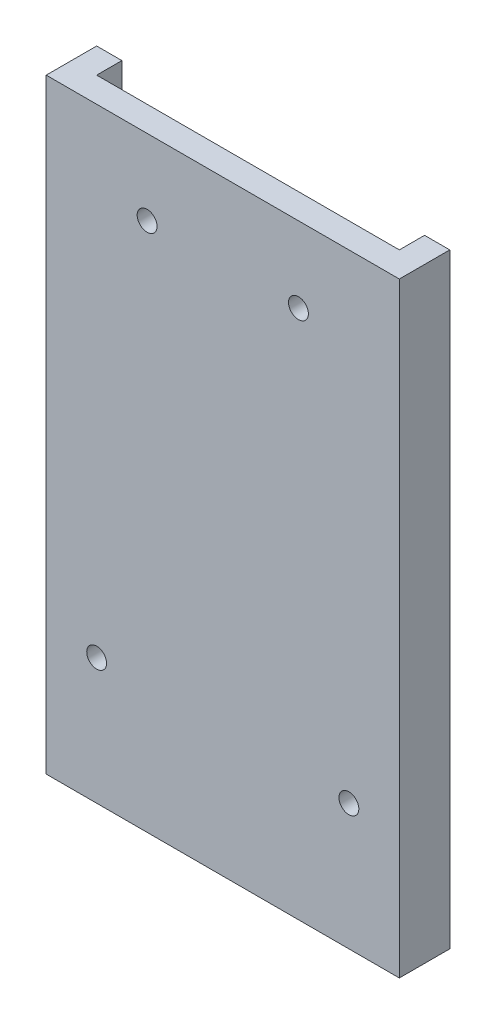
SolidWorks part; units mm, degrees
material "ABS"
ref_plane "Front" through (0, 0, 0) normal (0, 0, 1) x (1, 0, 0)
ref_plane "Top" through (0, 0, 0) normal (0, 1, 0) x (1, 0, 0)
ref_plane "Right" through (0, 0, 0) normal (1, 0, 0) x (0, 0, -1)
sketch "Sketch1" plane through (0, 0, 0) normal (0, 1, 0) x (1, 0, 0)
  line L1 (-22.225, 3.175) -> (22.225, 3.175)
  line L2 (-22.225, 3.175) -> (-22.225, -3.175)
  line L3 (-22.225, -3.175) -> (22.225, -3.175)
  line L4 (22.225, 3.175) -> (22.225, -3.175)
  line L5 (-22.225, 3.175) -> (22.225, -3.175) construction
  line L6 (-22.225, -3.175) -> (22.225, 3.175) construction
  point P0 (0, 0)
  dimension "D1" = 44.45
  dimension "D2" = 6.35
extrude "Boss-Extrude1" add sketch "Sketch1" along normal blind 76.2
sketch "Sketch2" plane through (0, 76.2, 0) normal (0, 1, 0) x (1, 0, 0)
  line L0 (22.225, 3.175) -> (-22.225, 3.175) construction
  line L1 (-19.05, 3.175) -> (19.05, 3.175)
  line L2 (-19.05, 3.175) -> (-19.05, 0)
  line L3 (-19.05, 0) -> (19.05, 0)
  line L4 (19.05, 3.175) -> (19.05, 0)
  dimension "D1" = 38.1
extrude "Cut-Extrude1" cut sketch "Sketch2" against normal offset from surface (73.025 mm away) 3.175 up to face at (0, 0, 0)
sketch "Sketch4" plane through (0, 0, 0) normal (0, 0, -1) x (-1, 0, 0)
  line L0 (-19.05, 15.875) -> (19.05, 15.875) construction
  line L1 (-19.05, 3.175) -> (-19.05, 76.2) construction
  line L2 (19.05, 3.175) -> (19.05, 76.2) construction
  line L3 (-19.05, 66.675) -> (19.05, 66.675) construction
  line L4 (19.05, 3.175) -> (19.05, 76.2) construction
  line L5 (-19.05, 3.175) -> (19.05, 3.175) construction
  line L6 (-15.875, 15.875) -> (-9.525, 66.675) construction
  line L7 (9.525, 66.675) -> (15.875, 15.875) construction
  line L8 (-12.7, 41.275) -> (12.7, 41.275) construction
  circle A0 centre (-9.525, 66.675) radius 1.25
  circle A1 centre (9.525, 66.675) radius 1.25
  circle A2 centre (-15.875, 15.875) radius 1.25
  circle A3 centre (15.875, 15.875) radius 1.25
  point P20 (0, 66.675)
  point P23 (0, 41.275)
  dimension "D3" = 2.5
  dimension "D1" = 50.8
  dimension "D2" = 12.7
  dimension "D4" = 19.05
  dimension "D5" = 31.75
extrude "Cut-Extrude2" cut sketch "Sketch4" against normal through all
